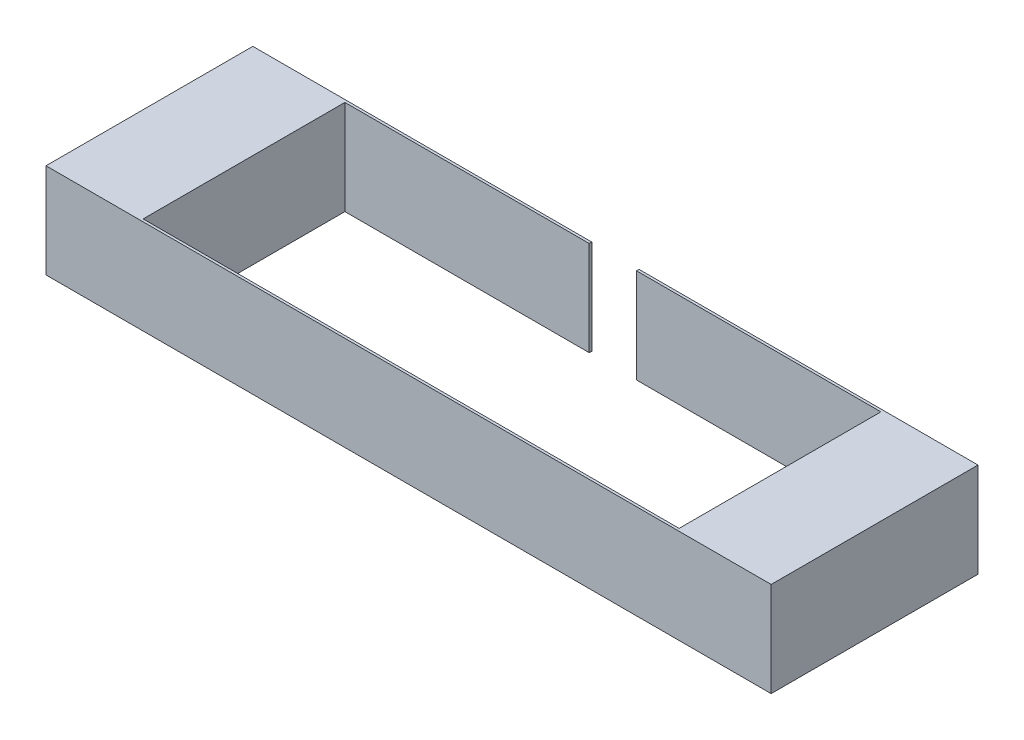
SolidWorks part; units mm, degrees
material "6061-T6 (SS)"
ref_plane "Front Plane" through (0, 0, 0) normal (0, 0, 1) x (1, 0, 0)
ref_plane "Top Plane" through (0, 0, 0) normal (0, 1, 0) x (1, 0, 0)
ref_plane "Right Plane" through (0, 0, 0) normal (1, 0, 0) x (0, 0, -1)
sketch "Sketch1" plane through (0, 0, 0) normal (1, 0, 0) x (0, 0, -1)
  line L0 (40.64, -19.05) -> (41.656, -19.05)
  line L1 (-41.656, -19.05) -> (-40.64, -19.05)
  line L2 (-41.656, -19.05) -> (-41.656, 19.05)
  line L3 (-41.656, 19.05) -> (-40.64, 19.05)
  line L4 (-40.64, -19.05) -> (-40.64, 19.05)
  line L5 (-41.656, -19.05) -> (-40.64, 19.05) construction
  line L6 (-41.656, 19.05) -> (-40.64, -19.05) construction
  line L7 (40.64, -19.05) -> (40.64, 19.05)
  line L8 (40.64, 19.05) -> (41.656, 19.05)
  line L9 (41.656, -19.05) -> (41.656, 19.05)
  line L10 (40.64, -19.05) -> (41.656, 19.05) construction
  line L11 (40.64, 19.05) -> (41.656, -19.05) construction
  line L12 (0, -1000) -> (0, 49000) construction
  point P0 (-41.148, 0)
  point P6 (41.148, 0)
  dimension "D1" = 1.016
  dimension "D2" = 38.1
  dimension "D3" = 40.64
extrude "Boss-Extrude2" add sketch "Sketch1" along normal mid plane 215.9
sketch "Sketch2" plane through (0, 0, 41.656) normal (0, 0, 1) x (1, 0, 0)
  line L0 (107.95, 19.05) -> (107.95, -19.05) construction
  line L1 (107.95, -19.05) -> (146.05, -19.05)
  line L2 (107.95, -19.05) -> (107.95, 19.05)
  line L3 (107.95, 19.05) -> (146.05, 19.05)
  line L4 (146.05, -19.05) -> (146.05, 19.05)
  dimension "D1" = 38.1
  dimension "D2" = 38.1
extrude "Boss-Extrude3" add sketch "Sketch2" against normal up to surface (83.312 mm away) up to face at (0, 0, -41.656)
mirror "Mirror4" about plane through (0, 0, 0) normal (1, 0, 0) of "Boss-Extrude3"
sketch "Sketch3" plane through (0, 0, -41.656) normal (0, 0, -1) x (-1, 0, 0)
  line L0 (146.05, 19.05) -> (-146.05, 19.05) construction
  line L1 (-9.525, -19.05) -> (9.525, -19.05)
  line L2 (-9.525, -19.05) -> (-9.525, 19.05)
  line L3 (-9.525, 19.05) -> (9.525, 19.05)
  line L4 (9.525, -19.05) -> (9.525, 19.05)
  line L5 (-9.525, -19.05) -> (9.525, 19.05) construction
  line L6 (-9.525, 19.05) -> (9.525, -19.05) construction
  point P0 (0, 0)
  dimension "D1" = 19.05
extrude "Cut-Extrude1" cut sketch "Sketch3" against normal up to next
